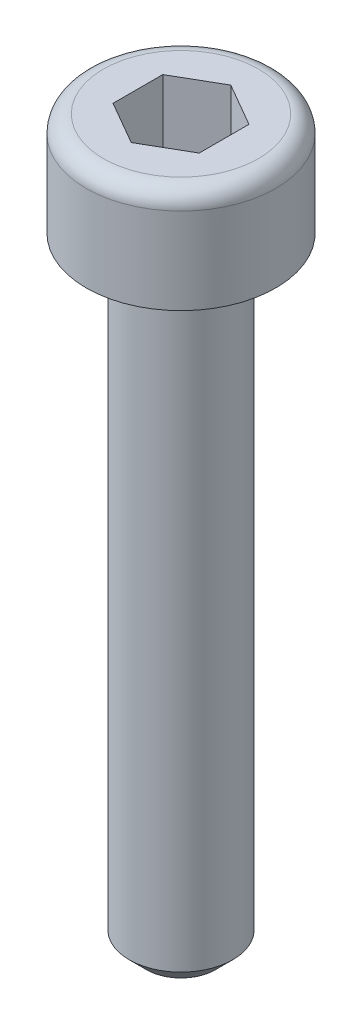
SolidWorks part; units mm, degrees
material "acero"
ref_plane "Alzado" through (0, 0, 0) normal (0, 0, 1) x (1, 0, 0)
ref_plane "Planta" through (0, 0, 0) normal (0, 1, 0) x (1, 0, 0)
ref_plane "Vista lateral" through (0, 0, 0) normal (1, 0, 0) x (0, 0, -1)
sketch "Croquis1" plane through (0, 0, 0) normal (0, 0, 1) x (1, 0, 0)
  line L0 (0, 0) -> (0, -60.9498) construction
  line L1 (0, 0) -> (2.75, 0)
  line L2 (2.75, 0) -> (2.75, -3)
  line L3 (2.75, -3) -> (1.5, -3)
  line L4 (1.5, -3) -> (1.5, -21)
  line L5 (1.5, -21) -> (0, -21)
  line L6 (0, -21) -> (0, 0)
  dimension "D1" = 18
  dimension "D2" = 3
  dimension "D3" = 5.5
  dimension "D4" = 3
revolve "Revolución1" add sketch "Croquis1" angle 360 about L0
sketch "Croquis2" plane through (0, 0, 0) normal (0, 1, 0) x (1, 0, 0)
  line L1 (1.25, 0.7217) -> (0, 1.4434)
  line L2 (0, 1.4434) -> (-1.25, 0.7217)
  line L3 (-1.25, 0.7217) -> (-1.25, -0.7217)
  line L4 (-1.25, -0.7217) -> (0, -1.4434)
  line L5 (0, -1.4434) -> (1.25, -0.7217)
  line L6 (1.25, -0.7217) -> (1.25, 0.7217)
  circle A0 centre (0, 0) radius 1.25 construction
  dimension "D1" = 2.5
extrude "Cortar-Extruir1" cut sketch "Croquis2" against normal blind 2
chamfer "Chaflán1" distance 0.5 angle 45 1 edges at (0, -21, 1.5)
fillet "Redondeo1" radius 0.5 1 edges at (0, 0, 2.75)
